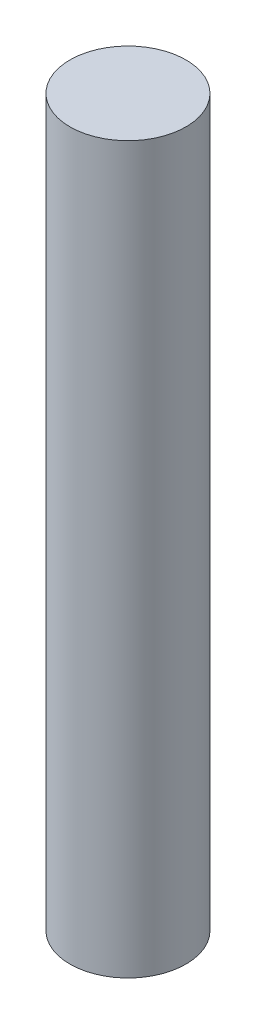
SolidWorks part; units mm, degrees
ref_plane "Front Plane" through (0, 0, 0) normal (0, 0, 1) x (1, 0, 0)
ref_plane "Top Plane" through (0, 0, 0) normal (0, 1, 0) x (1, 0, 0)
ref_plane "Right Plane" through (0, 0, 0) normal (1, 0, 0) x (0, 0, -1)
sketch "Sketch1" plane through (0, 0, 0) normal (0, 1, 0) x (1, 0, 0)
  circle A0 centre (0, 0) radius 4
  dimension "D1" = 8
extrude "Boss-Extrude1" add sketch "Sketch1" along normal mid plane 50
ref_plane "Plane1" through (0, -12.7594, 0) normal (0, 1, 0) x (1, 0, 0)
sketch "Sketch2" plane through (0, -12.7594, 0) normal (0, 1, 0) x (1, 0, 0)
  line L1 (0, 11.1429) -> (-9.65, 5.5714)
  line L2 (-9.65, 5.5714) -> (-9.65, -5.5714)
  line L3 (-9.65, -5.5714) -> (0, -11.1429)
  line L4 (0, -11.1429) -> (9.65, -5.5714)
  line L5 (9.65, -5.5714) -> (9.65, 5.5714)
  line L6 (9.65, 5.5714) -> (0, 11.1429)
  circle A0 centre (0, 0) radius 9.65 construction
  circle A1 centre (0, 0) radius 4
  circle A2 centre (0, 0) radius 4 construction
  dimension "D1" = 19.3
